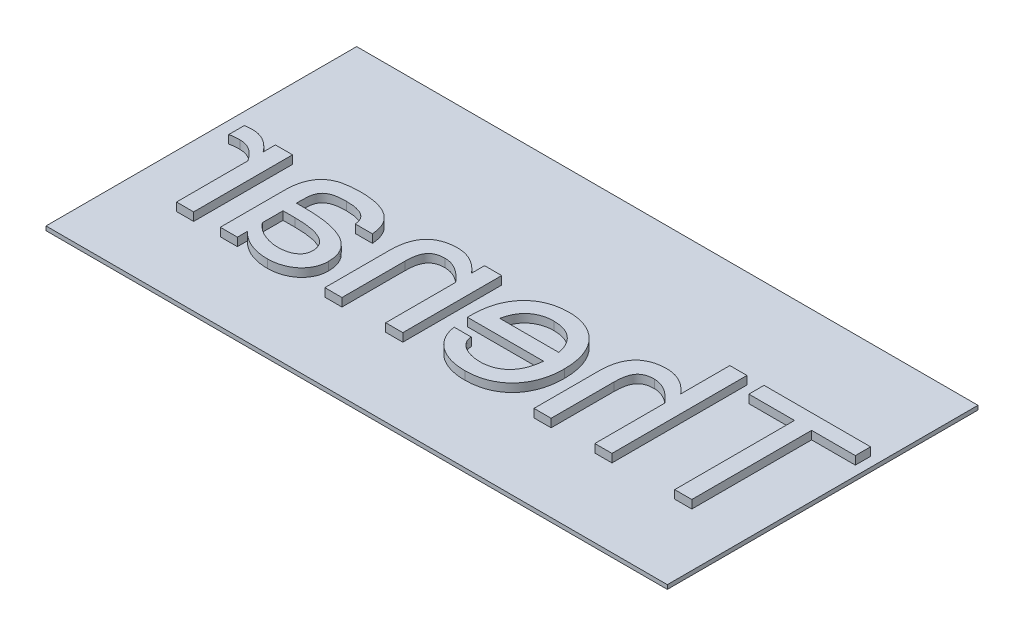
SolidWorks part; units mm, degrees
ref_plane "Front Plane" through (0, 0, 0) normal (0, 0, 1) x (1, 0, 0)
ref_plane "Top Plane" through (0, 0, 0) normal (0, 1, 0) x (1, 0, 0)
ref_plane "Right Plane" through (0, 0, 0) normal (1, 0, 0) x (0, 0, -1)
sketch "Sketch1" plane through (0, 0, 0) normal (0, 1, 0) x (1, 0, 0)
  line L1 (-15, 7.5) -> (15, 7.5)
  line L2 (-15, 7.5) -> (-15, -7.5)
  line L3 (-15, -7.5) -> (15, -7.5)
  line L4 (15, 7.5) -> (15, -7.5)
  line L5 (-15, 7.5) -> (15, -7.5) construction
  line L6 (-15, -7.5) -> (15, 7.5) construction
  point P0 (0, 0)
  dimension "D1" = 15
  dimension "D2" = 30
extrude "Boss-Extrude1" add sketch "Sketch1" along normal blind 0.2
sketch "Sketch2" plane through (0, 0.2, 0) normal (0, 1, 0) x (1, 0, 0)
  text T0 "Thenar" font "Gautami" height in points 20
extrude "Boss-Extrude2" add sketch "Sketch2" along normal blind 0.4
